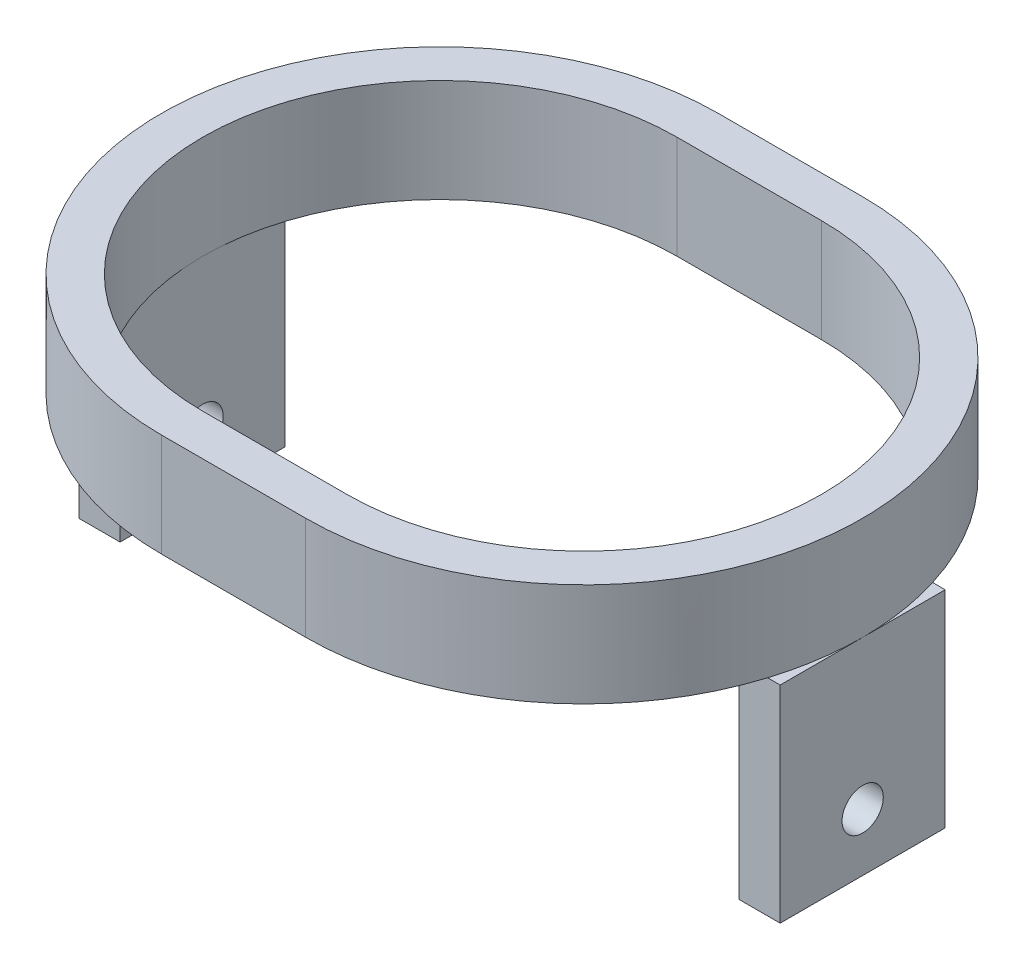
SolidWorks part; units mm, degrees
ref_plane "Front" through (0, 0, 0) normal (0, 0, 1) x (1, 0, 0)
ref_plane "Top" through (0, 0, 0) normal (0, 1, 0) x (1, 0, 0)
ref_plane "Right" through (0, 0, 0) normal (1, 0, 0) x (0, 0, -1)
sketch "草图2" plane through (0, 0, 0) normal (0, 1, 0) x (1, 0, 0)
  line L0 (-7, 0) -> (7, 0) construction
  line L1 (-7, 23) -> (7, 23)
  line L2 (-7, -23) -> (7, -23)
  line L3 (-7, 0) -> (7, 0) construction
  line L4 (-7, 27) -> (7, 27)
  line L5 (-7, -27) -> (7, -27)
  line L6 (-38.2984, -16) -> (-28.7486, -16) construction
  line L8 (-35.4759, -14) -> (-30.0868, -14) construction
  line L10 (16.7062, -14) -> (35.6561, -14) construction
  line L11 (23.5227, -16) -> (40.8516, -16) construction
  arc A4 (-7, 27) -> (-7, -27) centre (-7, 0) ccw
  arc A5 (7, -27) -> (7, 27) centre (7, 0) ccw
  arc A9 (-7, 23) -> (-7, -23) centre (-7, 0) ccw
  arc A10 (7, -23) -> (7, 23) centre (7, 0) ccw
  point P3 (0, 0)
  point P10 (0, 0)
  dimension "D1" = 16
extrude "凸台-拉伸1" add sketch "草图2" along normal blind 10
sketch "草图3" plane through (0, 0, 0) normal (0, -1, 0) x (1, 0, 0)
  line L1 (-34, 8) -> (-30, 8)
  line L2 (-34, 8) -> (-34, -8)
  line L3 (-34, -8) -> (-30, -8)
  line L4 (-30, 8) -> (-30, -8)
  line L5 (34, 8) -> (30, 8)
  line L6 (34, 8) -> (34, -8)
  line L7 (34, -8) -> (30, -8)
  line L8 (30, 8) -> (30, -8)
  dimension "D1" = 16
  dimension "D2" = 8
  dimension "D3" = 4
  dimension "D4" = 4
extrude "凸台-拉伸2" add sketch "草图3" along normal blind 20
sketch "草图5" plane through (34, 0, 0) normal (1, 0, 0) x (0, 0, -1)
  circle A0 centre (0, -14.4265) radius 2
extrude "切除-拉伸2" cut sketch "草图5" against normal through all
